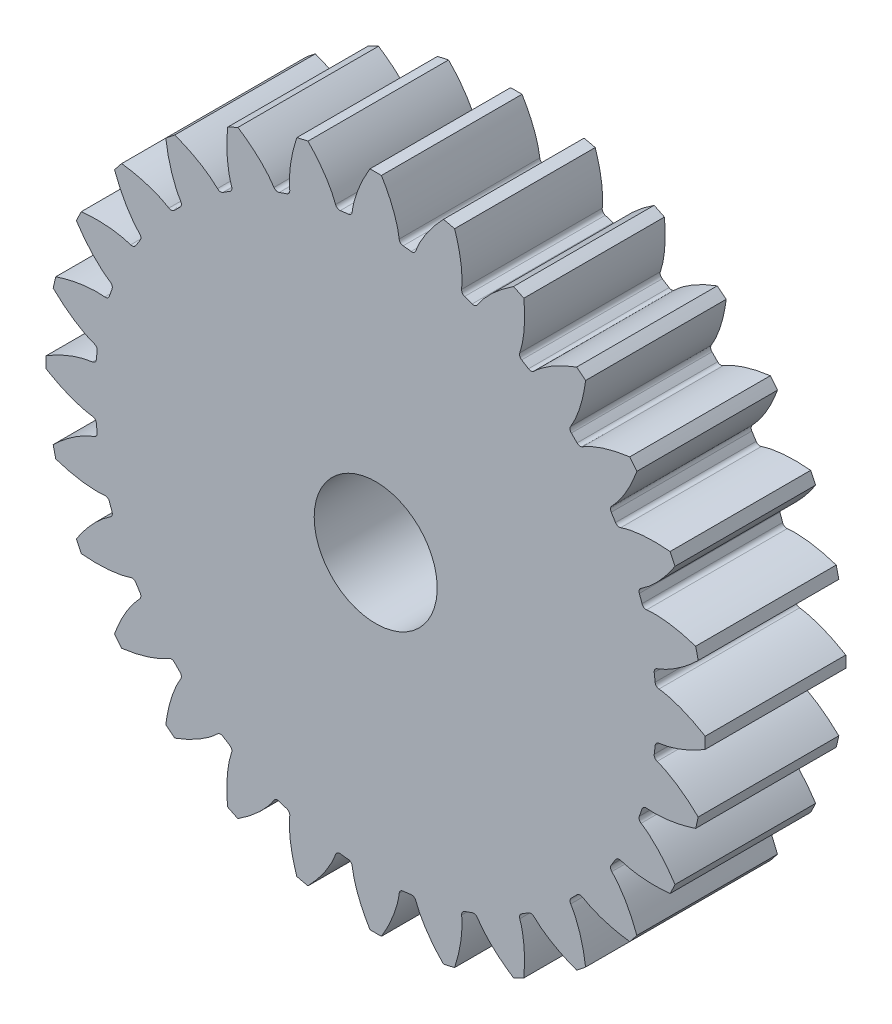
SolidWorks part; units mm, degrees
ref_plane "Alzado" through (0, 0, 0) normal (0, 0, 1) x (1, 0, 0)
ref_plane "Planta" through (0, 0, 0) normal (0, 1, 0) x (1, 0, 0)
ref_plane "Vista lateral" through (0, 0, 0) normal (1, 0, 0) x (0, 0, -1)
ref_plane "Plano1" through (0, 0, 16) normal (0, 0, 1) x (1, 0, 0)
sketch "Croquis1" plane through (0, 0, 16) normal (0, 0, 1) x (1, 0, 0)
  circle A0 centre (-5, 0) radius 7
  arc A1 (26.6939, -4.0312) -> (26.7963, -3.1223) centre (-5, 0) ccw
  arc A2 (26.7963, -3.1223) -> (27.2364, -2.6745) centre (27.2943, -3.1716) cw
  arc A3 (32.4943, -0.6523) -> (32.4943, 0.6524) centre (-5, 0) ccw
  arc A4 (27.2364, 2.6747) -> (26.7963, 3.1224) centre (27.2943, 3.1717) cw
  arc A5 (26.7963, 3.1224) -> (26.6939, 4.0313) centre (-5, 0) ccw
  arc A6 (26.6939, 4.0313) -> (27.0233, 4.5657) centre (27.1904, 4.094) cw
  arc A7 (31.6994, 7.7073) -> (31.4091, 8.9793) centre (-5, 0) ccw
  arc A8 (25.833, 9.7809) -> (25.3043, 10.1195) centre (25.7789, 10.2784) cw
  arc A9 (25.3043, 10.1195) -> (25.0022, 10.9827) centre (-5, 0) ccw
  arc A10 (25.0022, 10.9827) -> (25.2044, 11.5771) centre (25.4724, 11.1544) cw
  arc A11 (29.0643, 15.6805) -> (28.4982, 16.8559) centre (-5, 0) ccw
  arc A12 (22.8835, 16.3966) -> (22.2927, 16.6091) centre (22.72, 16.8697) cw
  arc A13 (22.2927, 16.6091) -> (21.8061, 17.3835) centre (-5, 0) ccw
  arc A14 (21.8061, 17.3835) -> (21.871, 18.008) centre (22.2263, 17.6555) cw
  arc A15 (24.721, 22.8674) -> (23.9075, 23.8874) centre (-5, 0) ccw
  arc A16 (18.5358, 22.1902) -> (17.9126, 22.2659) centre (18.2712, 22.615) cw
  arc A17 (17.9126, 22.2659) -> (17.2659, 22.9126) centre (-5, 0) ccw
  arc A18 (17.2659, 22.9126) -> (17.1902, 23.5358) centre (17.615, 23.2712) cw
  arc A19 (18.8874, 28.9076) -> (17.8673, 29.721) centre (-5, 0) ccw
  arc A20 (13.008, 26.871) -> (12.3835, 26.8062) centre (12.6554, 27.2263) cw
  arc A21 (12.3835, 26.8062) -> (11.6091, 27.2927) centre (-5, 0) ccw
  arc A22 (11.6091, 27.2927) -> (11.3966, 27.8835) centre (11.8696, 27.7201) cw
  arc A23 (11.8559, 33.4982) -> (10.6805, 34.0643) centre (-5, 0) ccw
  arc A24 (6.5771, 30.2045) -> (5.9827, 30.0023) centre (6.1544, 30.4724) cw
  arc A25 (5.9827, 30.0023) -> (5.1195, 30.3043) centre (-5, 0) ccw
  arc A26 (5.1195, 30.3043) -> (4.7808, 30.833) centre (5.2784, 30.7789) cw
  arc A27 (3.9793, 36.4091) -> (2.7073, 36.6995) centre (-5, 0) ccw
  arc A28 (-0.4343, 32.0233) -> (-0.9688, 31.6939) centre (-0.906, 32.1904) cw
  arc A29 (-0.9688, 31.6939) -> (-1.8776, 31.7963) centre (-5, 0) ccw
  arc A30 (-1.8776, 31.7963) -> (-2.3254, 32.2364) centre (-1.8283, 32.2944) cw
  arc A31 (-4.3477, 37.4944) -> (-5.6523, 37.4944) centre (-5, 0) ccw
  arc A32 (-7.6746, 32.2364) -> (-8.1224, 31.7963) centre (-8.1717, 32.2944) cw
  arc A33 (-8.1224, 31.7963) -> (-9.0312, 31.6939) centre (-5, 0) ccw
  arc A34 (-9.0312, 31.6939) -> (-9.5657, 32.0233) centre (-9.0939, 32.1905) cw
  arc A35 (-12.7073, 36.6995) -> (-13.9792, 36.4091) centre (-5, 0) ccw
  arc A36 (-14.7808, 30.833) -> (-15.1195, 30.3043) centre (-15.2784, 30.7789) cw
  arc A37 (-15.1195, 30.3043) -> (-15.9827, 30.0023) centre (-5, 0) ccw
  arc A38 (-15.9827, 30.0023) -> (-16.5771, 30.2045) centre (-16.1543, 30.4724) cw
  arc A39 (-20.6804, 34.0643) -> (-21.8559, 33.4982) centre (-5, 0) ccw
  arc A40 (-21.3966, 27.8835) -> (-21.6091, 27.2927) centre (-21.8697, 27.7201) cw
  arc A41 (-21.6091, 27.2927) -> (-22.3835, 26.8062) centre (-5, 0) ccw
  arc A42 (-22.3835, 26.8062) -> (-23.0079, 26.871) centre (-22.6554, 27.2263) cw
  arc A43 (-27.8673, 29.721) -> (-28.8873, 28.9076) centre (-5, 0) ccw
  arc A44 (-27.1901, 23.5358) -> (-27.2659, 22.9126) centre (-27.615, 23.2712) cw
  arc A45 (-27.2659, 22.9126) -> (-27.9126, 22.2659) centre (-5, 0) ccw
  arc A46 (-27.9126, 22.2659) -> (-28.5358, 22.1902) centre (-28.2712, 22.615) cw
  arc A47 (-33.9075, 23.8874) -> (-34.721, 22.8674) centre (-5, 0) ccw
  arc A48 (-31.871, 18.008) -> (-31.8061, 17.3835) centre (-32.2263, 17.6555) cw
  arc A49 (-31.8061, 17.3835) -> (-32.2927, 16.6091) centre (-5, 0) ccw
  arc A50 (-32.2927, 16.6091) -> (-32.8835, 16.3966) centre (-32.72, 16.8697) cw
  arc A51 (-38.4982, 16.8559) -> (-39.0643, 15.6805) centre (-5, 0) ccw
  arc A52 (-35.2044, 11.5771) -> (-35.0022, 10.9827) centre (-35.4724, 11.1544) cw
  arc A53 (-35.0022, 10.9827) -> (-35.3043, 10.1195) centre (-5, 0) ccw
  arc A54 (-35.3043, 10.1195) -> (-35.833, 9.7809) centre (-35.7789, 10.2784) cw
  arc A55 (-41.4091, 8.9793) -> (-41.6994, 7.7073) centre (-5, 0) ccw
  arc A56 (-37.0233, 4.5657) -> (-36.6939, 4.0313) centre (-37.1904, 4.094) cw
  arc A57 (-36.6939, 4.0313) -> (-36.7963, 3.1224) centre (-5, 0) ccw
  arc A58 (-36.7963, 3.1224) -> (-37.2364, 2.6747) centre (-37.2943, 3.1718) cw
  arc A59 (-42.4943, 0.6524) -> (-42.4943, -0.6523) centre (-5, 0) ccw
  arc A60 (-37.2364, -2.6746) -> (-36.7963, -3.1224) centre (-37.2943, -3.1717) cw
  arc A61 (-36.7963, -3.1224) -> (-36.6939, -4.0312) centre (-5, 0) ccw
  arc A62 (-36.6939, -4.0312) -> (-37.0233, -4.5657) centre (-37.1904, -4.0939) cw
  arc A63 (-41.6994, -7.7073) -> (-41.4091, -8.9792) centre (-5, 0) ccw
  arc A64 (-35.833, -9.7808) -> (-35.3043, -10.1194) centre (-35.7789, -10.2784) cw
  arc A65 (-35.3043, -10.1194) -> (-35.0022, -10.9827) centre (-5, 0) ccw
  arc A66 (-35.0022, -10.9827) -> (-35.2044, -11.5771) centre (-35.4724, -11.1543) cw
  arc A67 (-39.0643, -15.6804) -> (-38.4982, -16.8559) centre (-5, 0) ccw
  arc A68 (-32.8835, -16.3965) -> (-32.2927, -16.609) centre (-32.72, -16.8696) cw
  arc A69 (-32.2927, -16.609) -> (-31.8061, -17.3834) centre (-5, 0) ccw
  arc A70 (-31.8061, -17.3834) -> (-31.871, -18.0079) centre (-32.2263, -17.6554) cw
  arc A71 (-34.721, -22.8673) -> (-33.9075, -23.8873) centre (-5, 0) ccw
  arc A72 (-28.5358, -22.1901) -> (-27.9126, -22.2658) centre (-28.2712, -22.615) cw
  arc A73 (-27.9126, -22.2658) -> (-27.2659, -22.9125) centre (-5, 0) ccw
  arc A74 (-27.2659, -22.9125) -> (-27.1901, -23.5358) centre (-27.615, -23.2712) cw
  arc A75 (-28.8873, -28.9075) -> (-27.8673, -29.7209) centre (-5, 0) ccw
  arc A76 (-23.0079, -26.871) -> (-22.3835, -26.8061) centre (-22.6554, -27.2263) cw
  arc A77 (-22.3835, -26.8061) -> (-21.6091, -27.2927) centre (-5, 0) ccw
  arc A78 (-21.6091, -27.2927) -> (-21.3966, -27.8835) centre (-21.8697, -27.72) cw
  arc A79 (-21.8559, -33.4982) -> (-20.6804, -34.0642) centre (-5, 0) ccw
  arc A80 (-16.5771, -30.2044) -> (-15.9827, -30.0022) centre (-16.1543, -30.4723) cw
  arc A81 (-15.9827, -30.0022) -> (-15.1195, -30.3043) centre (-5, 0) ccw
  arc A82 (-15.1195, -30.3043) -> (-14.7808, -30.8329) centre (-15.2784, -30.7789) cw
  arc A83 (-13.9792, -36.4091) -> (-12.7073, -36.6994) centre (-5, 0) ccw
  arc A84 (-9.5657, -32.0233) -> (-9.0312, -31.6939) centre (-9.0939, -32.1904) cw
  arc A85 (-9.0312, -31.6939) -> (-8.1224, -31.7963) centre (-5, 0) ccw
  arc A86 (-8.1224, -31.7963) -> (-7.6746, -32.2363) centre (-8.1717, -32.2943) cw
  arc A87 (-5.6523, -37.4943) -> (-4.3477, -37.4943) centre (-5, 0) ccw
  arc A88 (-2.3254, -32.2363) -> (-1.8776, -31.7963) centre (-1.8283, -32.2943) cw
  arc A89 (-1.8776, -31.7963) -> (-0.9688, -31.6939) centre (-5, 0) ccw
  arc A90 (-0.9688, -31.6939) -> (-0.4343, -32.0233) centre (-0.906, -32.1904) cw
  arc A91 (2.7073, -36.6994) -> (3.9793, -36.4091) centre (-5, 0) ccw
  arc A92 (4.7808, -30.8329) -> (5.1195, -30.3043) centre (5.2784, -30.7788) cw
  arc A93 (5.1195, -30.3043) -> (5.9827, -30.0022) centre (-5, 0) ccw
  arc A94 (5.9827, -30.0022) -> (6.5771, -30.2044) centre (6.1544, -30.4723) cw
  arc A95 (10.6805, -34.0642) -> (11.8559, -33.4982) centre (-5, 0) ccw
  arc A96 (11.3966, -27.8835) -> (11.6091, -27.2927) centre (11.8696, -27.72) cw
  arc A97 (11.6091, -27.2927) -> (12.3835, -26.8061) centre (-5, 0) ccw
  arc A98 (12.3835, -26.8061) -> (13.008, -26.871) centre (12.6554, -27.2262) cw
  arc A99 (17.8673, -29.7209) -> (18.8874, -28.9075) centre (-5, 0) ccw
  arc A100 (17.1902, -23.5358) -> (17.2659, -22.9125) centre (17.615, -23.2712) cw
  arc A101 (17.2659, -22.9125) -> (17.9126, -22.2658) centre (-5, 0) ccw
  arc A102 (17.9126, -22.2658) -> (18.5358, -22.1901) centre (18.2712, -22.6149) cw
  arc A103 (23.9075, -23.8873) -> (24.721, -22.8673) centre (-5, 0) ccw
  arc A104 (21.871, -18.0079) -> (21.8061, -17.3834) centre (22.2263, -17.6554) cw
  arc A105 (21.8061, -17.3834) -> (22.2927, -16.609) centre (-5, 0) ccw
  arc A106 (22.2927, -16.609) -> (22.8835, -16.3965) centre (22.72, -16.8696) cw
  arc A107 (28.4982, -16.8559) -> (29.0643, -15.6804) centre (-5, 0) ccw
  arc A108 (25.2044, -11.5771) -> (25.0022, -10.9827) centre (25.4724, -11.1543) cw
  arc A109 (25.0022, -10.9827) -> (25.3043, -10.1194) centre (-5, 0) ccw
  arc A110 (25.3043, -10.1194) -> (25.833, -9.7808) centre (25.7789, -10.2783) cw
  arc A111 (31.4091, -8.9792) -> (31.6994, -7.7073) centre (-5, 0) ccw
  arc A112 (27.0233, -4.5657) -> (26.6939, -4.0312) centre (27.1904, -4.0939) cw
  ellipse E0 centre (31.3632, 3.1922) end of major axis (38.5176, 8.2016) minor radius 3.8394 (27.2364, -2.6745) -> (32.4943, -0.6523) ccw
  ellipse E1 centre (31.3267, -3.0695) end of major axis (38.4068, -7.967) minor radius 3.7593 (32.4943, 0.6524) -> (27.2364, 2.6747) ccw
  ellipse E2 centre (29.7412, 11.2037) end of major axis (23.8809, 4.7279) minor radius 3.8394 (27.0233, 4.5657) -> (31.6994, 7.7073) ccw
  ellipse E3 centre (31.0989, 5.0909) end of major axis (39.0914, 1.8916) minor radius 3.7593 (31.4091, 8.9793) -> (25.833, 9.7809) ccw
  ellipse E4 centre (26.3771, 18.6534) end of major axis (22.1048, 11.036) minor radius 3.8394 (25.2044, 11.5771) -> (29.0643, 15.6805) ccw
  ellipse E5 centre (29.061, 12.9961) end of major axis (37.565, 11.6554) minor radius 3.7593 (28.4982, 16.8559) -> (22.8835, 16.3966) ccw
  ellipse E6 centre (21.4397, 25.1678) end of major axis (23.9098, 33.545) minor radius 3.8394 (21.871, 18.008) -> (24.721, 22.8674) ccw
  ellipse E7 centre (25.3152, 20.2495) end of major axis (16.7261, 19.6642) minor radius 3.7593 (23.9075, 23.8874) -> (18.5358, 22.1902) ccw
  ellipse E8 centre (15.1764, 30.4202) end of major axis (14.6323, 21.7034) minor radius 3.8394 (17.1902, 23.5358) -> (18.8874, 28.9076) ccw
  ellipse E9 centre (20.0492, 26.4876) end of major axis (28.2926, 28.9694) minor radius 3.7593 (17.8673, 29.721) -> (13.008, 26.871) ccw
  ellipse E10 centre (7.9014, 34.1472) end of major axis (9.3106, 25.5278) minor radius 3.8394 (11.3966, 27.8835) -> (11.8559, 33.4982) ccw
  ellipse E11 centre (13.5271, 31.3974) end of major axis (6.0426, 27.1434) minor radius 3.7593 (10.6805, 34.0643) -> (6.5771, 30.2045) ccw
  ellipse E12 centre (-0.0205, 36.1619) end of major axis (3.2713, 28.0722) minor radius 3.8394 (4.7808, 30.833) -> (3.9793, 36.4091) ccw
  ellipse E13 centre (6.076, 34.7329) end of major axis (12.4263, 40.5457) minor radius 3.7593 (2.7073, 36.6995) -> (-0.4343, 32.0233) ccw
  ellipse E14 centre (-8.1921, 36.3632) end of major axis (-13.2015, 43.5176) minor radius 3.8394 (-2.3254, 32.2364) -> (-4.3477, 37.4944) ccw
  ellipse E15 centre (-1.9305, 36.3267) end of major axis (-6.8281, 29.2466) minor radius 3.7593 (-5.6523, 37.4944) -> (-7.6746, 32.2364) ccw
  ellipse E16 centre (-16.2037, 34.7412) end of major axis (-9.7278, 28.881) minor radius 3.8394 (-9.5657, 32.0233) -> (-12.7073, 36.6995) ccw
  ellipse E17 centre (-10.0909, 36.099) end of major axis (-6.8916, 44.0914) minor radius 3.7593 (-13.9792, 36.4091) -> (-14.7808, 30.833) ccw
  ellipse E18 centre (-23.6534, 31.3771) end of major axis (-16.0359, 27.1048) minor radius 3.8394 (-16.5771, 30.2045) -> (-20.6804, 34.0643) ccw
  ellipse E19 centre (-17.996, 34.0611) end of major axis (-19.3366, 25.5571) minor radius 3.7593 (-21.8559, 33.4982) -> (-21.3966, 27.8835) ccw
  ellipse E20 centre (-30.1678, 26.4397) end of major axis (-21.7906, 23.9695) minor radius 3.8394 (-23.0079, 26.871) -> (-27.8673, 29.721) ccw
  ellipse E21 centre (-25.2495, 30.3152) end of major axis (-24.6642, 21.7261) minor radius 3.7593 (-28.8873, 28.9076) -> (-27.1901, 23.5358) ccw
  ellipse E22 centre (-35.4202, 20.1764) end of major axis (-26.7033, 19.6323) minor radius 3.8394 (-28.5358, 22.1902) -> (-33.9075, 23.8874) ccw
  ellipse E23 centre (-31.4875, 25.0492) end of major axis (-33.9694, 33.2927) minor radius 3.7593 (-34.721, 22.8674) -> (-31.871, 18.008) ccw
  ellipse E24 centre (-39.1471, 12.9014) end of major axis (-30.5278, 14.3106) minor radius 3.8394 (-32.8835, 16.3966) -> (-38.4982, 16.8559) ccw
  ellipse E25 centre (-36.3974, 18.5271) end of major axis (-32.1434, 11.0426) minor radius 3.7593 (-39.0643, 15.6805) -> (-35.2044, 11.5771) ccw
  ellipse E26 centre (-41.1618, 4.9795) end of major axis (-33.0722, 8.2714) minor radius 3.8394 (-35.833, 9.7809) -> (-41.4091, 8.9793) ccw
  ellipse E27 centre (-39.7329, 11.076) end of major axis (-33.9201, 4.7258) minor radius 3.7593 (-41.6994, 7.7073) -> (-37.0233, 4.5657) ccw
  ellipse E28 centre (-41.3632, -3.1921) end of major axis (-48.5176, -8.2015) minor radius 3.8394 (-37.2364, 2.6747) -> (-42.4943, 0.6524) ccw
  ellipse E29 centre (-41.3267, 3.0695) end of major axis (-34.2465, -1.828) minor radius 3.7593 (-42.4943, -0.6523) -> (-37.2364, -2.6746) ccw
  ellipse E30 centre (-39.7412, -11.2036) end of major axis (-45.6015, -17.6795) minor radius 3.8394 (-37.0233, -4.5657) -> (-41.6994, -7.7073) ccw
  ellipse E31 centre (-41.0989, -5.0909) end of major axis (-49.0913, -1.8916) minor radius 3.7593 (-41.4091, -8.9792) -> (-35.833, -9.7808) ccw
  ellipse E32 centre (-36.3771, -18.6534) end of major axis (-40.6494, -26.2709) minor radius 3.8394 (-35.2044, -11.5771) -> (-39.0643, -15.6804) ccw
  ellipse E33 centre (-39.061, -12.996) end of major axis (-30.5571, -14.3366) minor radius 3.7593 (-38.4982, -16.8559) -> (-32.8835, -16.3965) ccw
  ellipse E34 centre (-31.4396, -25.1678) end of major axis (-28.9695, -16.7906) minor radius 3.8394 (-31.871, -18.0079) -> (-34.721, -22.8673) ccw
  ellipse E35 centre (-35.3151, -20.2494) end of major axis (-26.7261, -19.6641) minor radius 3.7593 (-33.9075, -23.8873) -> (-28.5358, -22.1901) ccw
  ellipse E36 centre (-25.1764, -30.4201) end of major axis (-25.7205, -39.1369) minor radius 3.8394 (-27.1901, -23.5358) -> (-28.8873, -28.9075) ccw
  ellipse E37 centre (-30.0492, -26.4875) end of major axis (-21.8057, -24.0056) minor radius 3.7593 (-27.8673, -29.7209) -> (-23.0079, -26.871) ccw
  ellipse E38 centre (-17.9014, -34.1471) end of major axis (-16.4922, -42.7664) minor radius 3.8394 (-21.3966, -27.8835) -> (-21.8559, -33.4982) ccw
  ellipse E39 centre (-23.5271, -31.3974) end of major axis (-16.0426, -27.1434) minor radius 3.7593 (-20.6804, -34.0642) -> (-16.5771, -30.2044) ccw
  ellipse E40 centre (-9.9795, -36.1618) end of major axis (-6.6876, -44.2515) minor radius 3.8394 (-14.7808, -30.8329) -> (-13.9792, -36.4091) ccw
  ellipse E41 centre (-16.076, -34.7328) end of major axis (-9.7257, -28.92) minor radius 3.7593 (-12.7073, -36.6994) -> (-9.5657, -32.0233) ccw
  ellipse E42 centre (-1.8079, -36.3632) end of major axis (3.2016, -43.5175) minor radius 3.8394 (-7.6746, -32.2363) -> (-5.6523, -37.4943) ccw
  ellipse E43 centre (-8.0695, -36.3266) end of major axis (-12.9671, -43.4068) minor radius 3.7593 (-4.3477, -37.4943) -> (-2.3254, -32.2363) ccw
  ellipse E44 centre (6.2037, -34.7412) end of major axis (-0.2721, -28.8809) minor radius 3.8394 (-0.4343, -32.0233) -> (2.7073, -36.6994) ccw
  ellipse E45 centre (0.0909, -36.0989) end of major axis (-3.1084, -44.0913) minor radius 3.7593 (3.9793, -36.4091) -> (4.7808, -30.8329) ccw
  ellipse E46 centre (13.6534, -31.3771) end of major axis (6.0359, -27.1047) minor radius 3.8394 (6.5771, -30.2044) -> (10.6805, -34.0642) ccw
  ellipse E47 centre (7.996, -34.061) end of major axis (6.6554, -42.5649) minor radius 3.7593 (11.8559, -33.4982) -> (11.3966, -27.8835) ccw
  ellipse E48 centre (20.1678, -26.4396) end of major axis (28.545, -28.9098) minor radius 3.8394 (13.008, -26.871) -> (17.8673, -29.7209) ccw
  ellipse E49 centre (15.2495, -30.3151) end of major axis (15.8348, -38.9042) minor radius 3.7593 (18.8874, -28.9075) -> (17.1902, -23.5358) ccw
  ellipse E50 centre (25.4202, -20.1764) end of major axis (34.137, -20.7205) minor radius 3.8394 (18.5358, -22.1901) -> (23.9075, -23.8873) ccw
  ellipse E51 centre (21.4875, -25.0491) end of major axis (19.0057, -16.8057) minor radius 3.7593 (24.721, -22.8673) -> (21.871, -18.0079) ccw
  ellipse E52 centre (29.1471, -12.9014) end of major axis (37.7665, -11.4922) minor radius 3.8394 (22.8835, -16.3965) -> (28.4982, -16.8559) ccw
  ellipse E53 centre (26.3974, -18.5271) end of major axis (30.6514, -26.0116) minor radius 3.7593 (29.0643, -15.6804) -> (25.2044, -11.5771) ccw
  ellipse E54 centre (31.1618, -4.9794) end of major axis (39.2515, -1.6876) minor radius 3.8394 (25.833, -9.7808) -> (31.4091, -8.9792) ccw
  ellipse E55 centre (29.7329, -11.076) end of major axis (23.9201, -4.7257) minor radius 3.7593 (31.6994, -7.7073) -> (27.0233, -4.5657) ccw
  point P6 (31.3632, 3.1922)
  point P7 (38.5175, 8.2016)
  point P8 (33.5653, 0.0471)
  point P9 (27.2364, -2.6747)
  point P10 (32.4943, -0.6523)
  point P11 (29.9042, -1.9543)
  point P12 (32.8222, 8.3386)
  point P20 (31.3267, -3.0695)
  point P21 (38.4068, -7.9671)
  point P22 (29.1881, -6.1612)
  point P23 (32.4943, 0.6523)
  point P24 (27.2364, 2.6746)
  point P25 (29.9042, 1.9543)
  point P26 (32.7491, -8.0934)
  point P38 (29.7412, 11.2037)
  point P39 (32.5879, 8.6275)
  point P40 (23.8809, 4.7279)
  point P41 (27.0233, 4.5657)
  point P42 (31.6994, 7.7073)
  point P43 (29.464, 5.8616)
  point P44 (30.0184, 16.5458)
  point P52 (31.0989, 5.0909)
  point P53 (39.0914, 1.8916)
  point P54 (29.7019, 1.6008)
  point P55 (31.4091, 8.9792)
  point P56 (25.833, 9.7808)
  point P57 (28.5942, 9.6722)
  point P58 (33.6036, 0.5095)
  point P70 (26.3771, 18.6534)
  point P71 (29.7257, 16.7753)
  point P72 (22.1048, 11.036)
  point P73 (25.2045, 11.5771)
  point P74 (29.0642, 15.6805)
  point P75 (27.2956, 13.3836)
  point P76 (25.4586, 23.9233)
  point P84 (29.061, 12.996)
  point P85 (37.565, 11.6554)
  point P86 (28.4756, 9.2826)
  point P87 (28.4982, 16.8559)
  point P88 (22.8835, 16.3965)
  point P89 (25.5997, 16.9051)
  point P90 (32.5224, 9.0868)
  point P102 (21.4396, 25.1678)
  point P103 (25.1222, 24.0819)
  point P104 (18.9695, 16.7906)
  point P105 (21.871, 18.0079)
  point P106 (24.7209, 22.8673)
  point P107 (23.5077, 20.2345)
  point P108 (19.3715, 30.1011)
  point P116 (25.3152, 20.2494)
  point P117 (33.9042, 20.8348)
  point P118 (25.5708, 16.4989)
  point P119 (23.9075, 23.8873)
  point P120 (18.5358, 22.1901)
  point P121 (21.0707, 23.2904)
  point P122 (29.5596, 17.2085)
  point P134 (15.1764, 30.4202)
  point P135 (19.0082, 30.181)
  point P136 (14.6322, 21.7034)
  point P137 (17.1902, 23.5358)
  point P138 (18.8873, 28.9075)
  point P139 (18.2904, 26.0707)
  point P140 (12.0624, 34.7696)
  point P148 (20.0492, 26.4875)
  point P149 (28.2926, 28.9694)
  point P150 (21.1329, 22.8878)
  point P151 (17.8673, 29.7209)
  point P152 (13.008, 26.871)
  point P153 (15.2345, 28.5077)
  point P154 (24.8639, 24.4673)
  point P166 (7.9014, 34.1471)
  point P167 (11.6904, 34.7666)
  point P168 (9.3106, 25.5278)
  point P169 (11.3966, 27.8835)
  point P170 (11.8559, 33.4982)
  point P171 (11.9051, 30.5997)
  point P172 (3.8976, 37.6946)
  point P180 (13.5271, 31.3974)
  point P181 (21.0116, 35.6514)
  point P182 (15.3847, 28.1291)
  point P183 (10.6805, 34.0642)
  point P184 (6.5771, 30.2044)
  point P185 (8.3836, 32.2956)
  point P186 (18.6706, 30.4992)
  point P198 (-0.0206, 36.1618)
  point P199 (3.5356, 37.6089)
  point P200 (3.2713, 28.0722)
  point P201 (4.7809, 30.833)
  point P202 (3.9792, 36.4091)
  point P203 (4.6722, 33.5942)
  point P204 (-4.7133, 38.7294)
  point P212 (6.076, 34.7328)
  point P213 (12.4263, 40.5457)
  point P214 (8.6143, 31.9599)
  point P215 (2.7073, 36.6994)
  point P216 (-0.4343, 32.0233)
  point P217 (0.8616, 34.464)
  point P218 (11.2904, 35.0017)
  point P230 (-8.1922, 36.3632)
  point P231 (-5.0471, 38.5653)
  point P232 (-3.1827, 29.2089)
  point P233 (-2.3253, 32.2364)
  point P234 (-4.3477, 37.4943)
  point P235 (-3.0457, 34.9042)
  point P236 (-13.3386, 37.8222)
  point P244 (-1.9305, 36.3267)
  point P245 (1.1612, 34.1881)
  point P246 (-6.828, 29.2465)
  point P247 (-5.6523, 37.4943)
  point P248 (-7.6746, 32.2364)
  point P249 (-6.9543, 34.9042)
  point P250 (3.0934, 37.7491)
  point P262 (-16.2037, 34.7412)
  point P263 (-9.7279, 28.8809)
  point P264 (-18.7799, 31.8944)
  point P265 (-9.5657, 32.0233)
  point P266 (-12.7073, 36.6994)
  point P267 (-10.8616, 34.464)
  point P268 (-21.5458, 35.0184)
  point P276 (-10.0909, 36.0989)
  point P277 (-6.6008, 34.7019)
  point P278 (-13.2902, 28.1065)
  point P279 (-13.9792, 36.4091)
  point P280 (-14.7808, 30.833)
  point P281 (-14.6722, 33.5942)
  point P282 (-5.5095, 38.6036)
  point P294 (-23.6534, 31.3771)
  point P295 (-16.036, 27.1048)
  point P296 (-25.5315, 28.0285)
  point P297 (-16.5771, 30.2045)
  point P298 (-20.6805, 34.0642)
  point P299 (-18.3836, 32.2956)
  point P300 (-28.9233, 30.4586)
  point P308 (-17.996, 34.061)
  point P309 (-14.2826, 33.4756)
  point P310 (-19.3366, 25.5571)
  point P311 (-21.8559, 33.4982)
  point P312 (-21.3965, 27.8835)
  point P313 (-21.9051, 30.5997)
  point P314 (-14.0868, 37.5224)
  point P326 (-30.1678, 26.4396)
  point P327 (-21.7906, 23.9695)
  point P328 (-31.2537, 22.757)
  point P329 (-23.0079, 26.871)
  point P330 (-27.8673, 29.7209)
  point P331 (-25.2345, 28.5077)
  point P332 (-35.1011, 24.3715)
  point P340 (-25.2494, 30.3152)
  point P341 (-21.4989, 30.5708)
  point P342 (-24.6641, 21.7261)
  point P343 (-28.8873, 28.9075)
  point P344 (-27.1901, 23.5358)
  point P345 (-28.2904, 26.0707)
  point P346 (-22.2085, 34.5596)
  point P358 (-35.4202, 20.1764)
  point P359 (-26.7034, 19.6322)
  point P360 (-35.6594, 16.3445)
  point P361 (-28.5358, 22.1902)
  point P362 (-33.9075, 23.8873)
  point P363 (-31.0707, 23.2904)
  point P364 (-39.7696, 17.0624)
  point P372 (-31.4875, 25.0492)
  point P373 (-27.8878, 26.1329)
  point P374 (-29.0056, 16.8057)
  point P375 (-34.7209, 22.8673)
  point P376 (-31.871, 18.008)
  point P377 (-33.5077, 20.2345)
  point P378 (-29.4673, 29.8639)
  point P390 (-39.1471, 12.9014)
  point P391 (-30.5278, 14.3106)
  point P392 (-38.5277, 9.1123)
  point P393 (-32.8835, 16.3966)
  point P394 (-38.4982, 16.8559)
  point P395 (-35.5997, 16.9051)
  point P396 (-42.6946, 8.8976)
  point P404 (-36.3974, 18.5271)
  point P405 (-33.1291, 20.3847)
  point P406 (-32.1434, 11.0426)
  point P407 (-39.0642, 15.6805)
  point P408 (-35.2044, 11.5771)
  point P409 (-37.2956, 13.3836)
  point P410 (-35.4992, 23.6706)
  point P422 (-41.1618, 4.9794)
  point P423 (-33.0722, 8.2713)
  point P424 (-39.7147, 1.4232)
  point P425 (-35.833, 9.7809)
  point P426 (-41.4091, 8.9792)
  point P427 (-38.5942, 9.6722)
  point P428 (-43.7294, 0.2867)
  point P436 (-39.7328, 11.076)
  point P437 (-36.9599, 13.6143)
  point P438 (-33.92, 4.7258)
  point P439 (-41.6994, 7.7073)
  point P440 (-37.0233, 4.5657)
  point P441 (-39.464, 5.8616)
  point P442 (-40.0017, 16.2904)
  point P454 (-41.3632, -3.1922)
  point P455 (-34.2089, 1.8173)
  point P456 (-39.1611, -6.3372)
  point P457 (-37.2364, 2.6747)
  point P458 (-42.4943, 0.6523)
  point P459 (-39.9042, 1.9543)
  point P460 (-42.8222, -8.3386)
  point P468 (-41.3267, 3.0695)
  point P469 (-34.2465, -1.828)
  point P470 (-43.4653, -0.0221)
  point P471 (-42.4943, -0.6523)
  point P472 (-37.2364, -2.6746)
  point P473 (-39.9042, -1.9543)
  point P474 (-42.7491, 8.0934)
  point P486 (-39.7412, -11.2037)
  point P487 (-36.8944, -13.7799)
  point P488 (-45.6014, -17.6795)
  point P489 (-37.0233, -4.5657)
  point P490 (-41.6994, -7.7073)
  point P491 (-39.464, -5.8616)
  point P492 (-40.0184, -16.5458)
  point P500 (-41.0989, -5.0909)
  point P501 (-33.1065, -8.2902)
  point P502 (-42.496, -8.5809)
  point P503 (-41.4091, -8.9792)
  point P504 (-35.833, -9.7808)
  point P505 (-38.5942, -9.6722)
  point P506 (-43.6036, -0.5095)
  point P518 (-36.3771, -18.6534)
  point P519 (-33.0285, -20.5315)
  point P520 (-40.6494, -26.2709)
  point P521 (-35.2045, -11.5771)
  point P522 (-39.0642, -15.6805)
  point P523 (-37.2956, -13.3836)
  point P524 (-35.4586, -23.9233)
  point P532 (-39.061, -12.996)
  point P533 (-30.5571, -14.3366)
  point P534 (-39.6464, -16.7094)
  point P535 (-38.4982, -16.8559)
  point P536 (-32.8835, -16.3965)
  point P537 (-35.5997, -16.9051)
  point P538 (-42.5224, -9.0868)
  point P550 (-31.4396, -25.1678)
  point P551 (-27.757, -26.2537)
  point P552 (-33.9098, -33.545)
  point P553 (-31.871, -18.0079)
  point P554 (-34.7209, -22.8673)
  point P555 (-33.5077, -20.2345)
  point P556 (-29.3715, -30.1011)
  point P564 (-35.3152, -20.2494)
  point P565 (-26.7261, -19.6641)
  point P566 (-35.0596, -24)
  point P567 (-33.9075, -23.8873)
  point P568 (-28.5358, -22.1901)
  point P569 (-31.0707, -23.2904)
  point P570 (-39.5596, -17.2085)
  point P582 (-25.1764, -30.4202)
  point P583 (-21.3445, -30.6594)
  point P584 (-25.7205, -39.137)
  point P585 (-27.1902, -23.5358)
  point P586 (-28.8873, -28.9075)
  point P587 (-28.2904, -26.0707)
  point P588 (-22.0624, -34.7696)
  point P596 (-30.0492, -26.4875)
  point P597 (-21.8057, -24.0056)
  point P598 (-28.9654, -30.0872)
  point P599 (-27.8673, -29.7209)
  point P600 (-23.008, -26.871)
  point P601 (-25.2345, -28.5077)
  point P602 (-34.8639, -24.4673)
  point P614 (-17.9014, -34.1471)
  point P615 (-14.1123, -33.5277)
  point P616 (-16.4922, -42.7665)
  point P617 (-21.3966, -27.8835)
  point P618 (-21.8559, -33.4982)
  point P619 (-21.9051, -30.5997)
  point P620 (-13.8976, -37.6946)
  point P628 (-23.5271, -31.3974)
  point P629 (-16.0426, -27.1434)
  point P630 (-21.6695, -34.6656)
  point P631 (-20.6805, -34.0642)
  point P632 (-16.5771, -30.2044)
  point P633 (-18.3836, -32.2956)
  point P634 (-28.6706, -30.4992)
  point P646 (-9.9794, -36.1618)
  point P647 (-6.4232, -34.7147)
  point P648 (-6.6876, -44.2515)
  point P649 (-14.7809, -30.833)
  point P650 (-13.9792, -36.4091)
  point P651 (-14.6722, -33.5942)
  point P652 (-5.2867, -38.7294)
  point P660 (-16.076, -34.7328)
  point P661 (-9.7258, -28.92)
  point P662 (-13.5378, -37.5058)
  point P663 (-12.7073, -36.6994)
  point P664 (-9.5657, -32.0233)
  point P665 (-10.8616, -34.464)
  point P666 (-21.2904, -35.0017)
  point P678 (-1.8078, -36.3632)
  point P679 (1.3372, -34.1611)
  point P680 (3.2016, -43.5175)
  point P681 (-7.6747, -32.2364)
  point P682 (-5.6523, -37.4943)
  point P683 (-6.9543, -34.9042)
  point P684 (3.3386, -37.8222)
  point P692 (-8.0695, -36.3267)
  point P693 (-4.9779, -38.4653)
  point P694 (-12.9671, -43.4068)
  point P695 (-4.3477, -37.4943)
  point P696 (-2.3254, -32.2364)
  point P697 (-3.0457, -34.9042)
  point P698 (-13.0934, -37.7491)
  point P710 (6.2037, -34.7412)
  point P711 (12.6795, -40.6014)
  point P712 (3.6275, -37.5879)
  point P713 (-0.4343, -32.0233)
  point P714 (2.7073, -36.6994)
  point P715 (0.8616, -34.464)
  point P716 (11.5458, -35.0184)
  point P724 (0.0909, -36.0989)
  point P725 (3.5809, -37.496)
  point P726 (-3.1084, -44.0914)
  point P727 (3.9792, -36.4091)
  point P728 (4.7808, -30.833)
  point P729 (4.6722, -33.5942)
  point P730 (-4.4905, -38.6036)
  point P742 (13.6534, -31.3771)
  point P743 (21.2709, -35.6494)
  point P744 (11.7753, -34.7257)
  point P745 (6.5771, -30.2045)
  point P746 (10.6805, -34.0642)
  point P747 (8.3836, -32.2956)
  point P748 (18.9233, -30.4586)
  point P756 (7.996, -34.061)
  point P757 (11.7094, -34.6464)
  point P758 (6.6554, -42.565)
  point P759 (11.8559, -33.4982)
  point P760 (11.3965, -27.8835)
  point P761 (11.9051, -30.5997)
  point P762 (4.0868, -37.5224)
  point P774 (20.1678, -26.4396)
  point P775 (28.545, -28.9098)
  point P776 (19.0819, -30.1222)
  point P777 (13.0079, -26.871)
  point P778 (17.8673, -29.7209)
  point P779 (15.2345, -28.5077)
  point P780 (25.1011, -24.3715)
  point P788 (15.2494, -30.3152)
  point P789 (19, -30.0596)
  point P790 (15.8348, -38.9042)
  point P791 (18.8873, -28.9075)
  point P792 (17.1901, -23.5358)
  point P793 (18.2904, -26.0707)
  point P794 (12.2085, -34.5596)
  point P806 (25.4202, -20.1764)
  point P807 (34.137, -20.7205)
  point P808 (25.181, -24.0082)
  point P809 (18.5358, -22.1902)
  point P810 (23.9075, -23.8873)
  point P811 (21.0707, -23.2904)
  point P812 (29.7696, -17.0624)
  point P820 (21.4875, -25.0492)
  point P821 (25.0872, -23.9654)
  point P822 (23.9694, -33.2926)
  point P823 (24.7209, -22.8673)
  point P824 (21.871, -18.008)
  point P825 (23.5077, -20.2345)
  point P826 (19.4673, -29.8639)
  point P838 (29.1471, -12.9014)
  point P839 (37.7665, -11.4922)
  point P840 (29.7666, -16.6904)
  point P841 (22.8835, -16.3966)
  point P842 (28.4982, -16.8559)
  point P843 (25.5997, -16.9051)
  point P844 (32.6946, -8.8976)
  point P852 (26.3974, -18.5271)
  point P853 (29.6656, -16.6695)
  point P854 (30.6514, -26.0116)
  point P855 (29.0642, -15.6805)
  point P856 (25.2044, -11.5771)
  point P857 (27.2956, -13.3836)
  point P858 (25.4992, -23.6706)
  point P870 (31.1618, -4.9794)
  point P871 (39.2515, -1.6876)
  point P872 (32.6089, -8.5356)
  point P873 (25.833, -9.7809)
  point P874 (31.4091, -8.9792)
  point P875 (28.5942, -9.6722)
  point P876 (33.7294, -0.2867)
  point P884 (29.7328, -11.076)
  point P885 (32.5058, -8.5378)
  point P886 (35.5457, -17.4263)
  point P887 (31.6994, -7.7073)
  point P888 (27.0233, -4.5657)
  point P889 (29.464, -5.8616)
  point P890 (30.0017, -16.2904)
extrude "Saliente-Extruir1" add sketch "Croquis1" against normal blind 16
